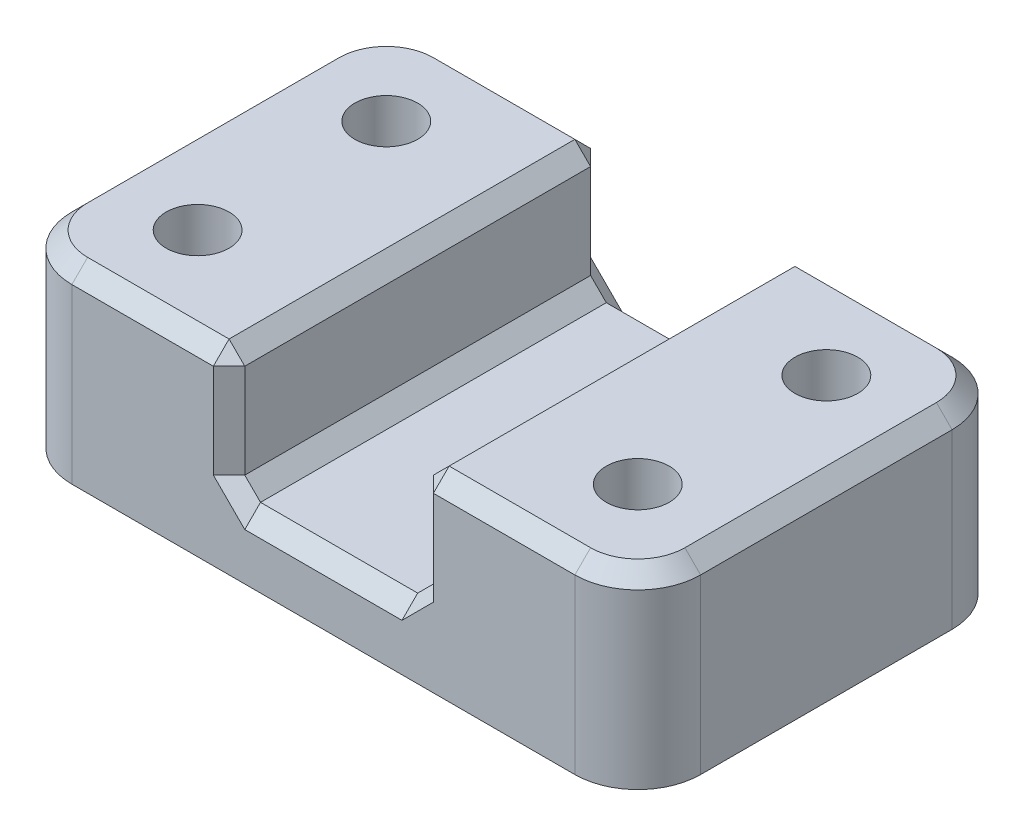
SolidWorks part; units mm, degrees
ref_plane "Front Plane" through (0, 0, 0) normal (0, 0, 1) x (1, 0, 0)
ref_plane "Top Plane" through (0, 0, 0) normal (0, 1, 0) x (1, 0, 0)
ref_plane "Right Plane" through (0, 0, 0) normal (1, 0, 0) x (0, 0, -1)
sketch "Sketch2" plane through (0, 0, 0) normal (0, 1, 0) x (1, 0, 0)
  line L0 (0, 56.9872) -> (0, -68.5326) construction
  line L1 (-63.5, 38.1) -> (63.5, 38.1)
  line L2 (-63.5, 38.1) -> (-63.5, -38.1)
  line L3 (-63.5, -38.1) -> (63.5, -38.1)
  line L4 (63.5, 38.1) -> (63.5, -38.1)
  line L5 (-63.5, 38.1) -> (63.5, -38.1) construction
  line L6 (-63.5, -38.1) -> (63.5, 38.1) construction
  line L7 (89.8473, 0) -> (-96.9522, 0) construction
  circle A0 centre (-44.45, 19.05) radius 6.35
  circle A1 centre (44.45, 19.05) radius 6.35
  circle A2 centre (44.45, -19.05) radius 6.35
  circle A3 centre (-44.45, -19.05) radius 6.35
  point P0 (0, 0)
  dimension "D3" = 12.7
  dimension "D1" = 127
  dimension "D2" = 76.2
  dimension "D4" = 19.05
  dimension "D5" = 19.05
extrude "Boss-Extrude1" add sketch "Sketch2" along normal blind 38.1
sketch "Sketch3" plane through (0, 38.1, 0) normal (0, 1, 0) x (1, 0, 0)
  line L0 (-63.5, -38.1) -> (63.5, -38.1) construction
  line L1 (-19.05, 38.1) -> (19.05, 38.1)
  line L2 (-19.05, 38.1) -> (-19.05, -38.1)
  line L3 (-19.05, -38.1) -> (19.05, -38.1)
  line L4 (19.05, 38.1) -> (19.05, -38.1)
  line L5 (-19.05, 38.1) -> (19.05, -38.1) construction
  line L6 (-19.05, -38.1) -> (19.05, 38.1) construction
  point P0 (0, 0)
  dimension "D1" = 38.1
extrude "Cut-Extrude1" cut sketch "Sketch3" against normal blind 25.4
fillet "Fillet1" radius 12.7 4 edges at (-63.5, 19.05, 38.1) (-63.5, 19.05, -38.1) (63.5, 19.05, -38.1) (63.5, 19.05, 38.1)
chamfer "Chamfer1" distance 3.175 angle 45 20 edges at (-19.05, 25.4, 38.1) (19.05, 25.4, 38.1) (-19.05, 25.4, -38.1) (19.05, 25.4, -38.1) (0, 12.7, 38.1) (-19.05, 12.7, 0) (0, 12.7, -38.1) (19.05, 12.7, 0) (-34.925, 38.1, 38.1) (-59.7803, 38.1, 34.3803) (-63.5, 38.1, 0) (-59.7803, 38.1, -34.3803) (-34.925, 38.1, -38.1) (-19.05, 38.1, 0) (34.925, 38.1, 38.1) (59.7803, 38.1, 34.3803) (63.5, 38.1, 0) (59.7803, 38.1, -34.3803) (19.05, 38.1, 0) (34.925, 38.1, -38.1)
